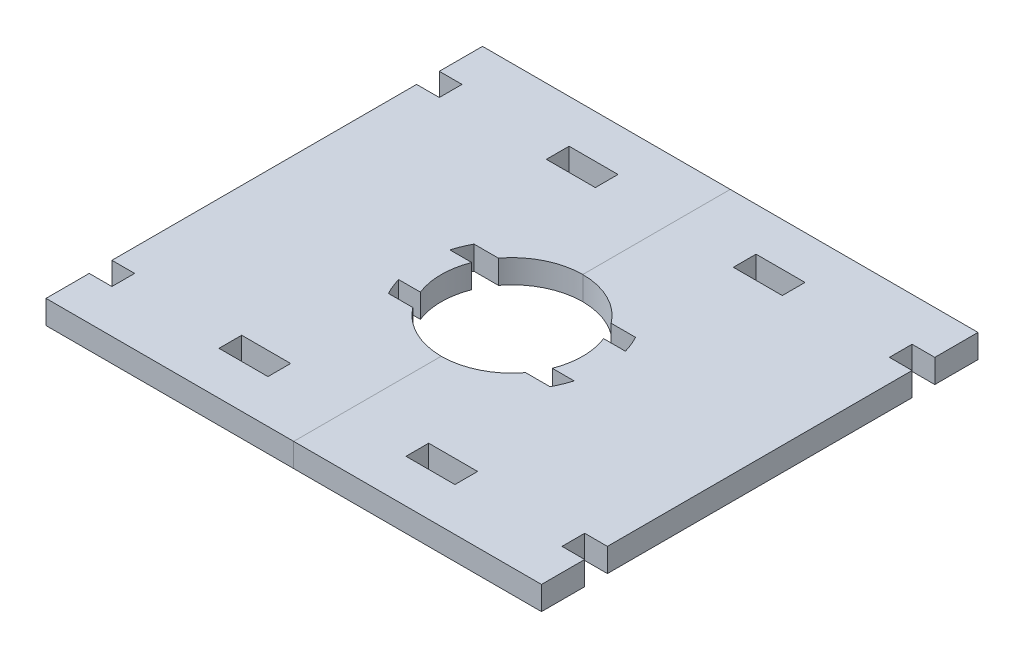
SolidWorks part; units mm, degrees
ref_plane "Front Plane" through (0, 0, 0) normal (0, 0, 1) x (1, 0, 0)
ref_plane "Top Plane" through (0, 0, 0) normal (0, 1, 0) x (1, 0, 0)
ref_plane "Right Plane" through (0, 0, 0) normal (1, 0, 0) x (0, 0, -1)
sketch "Sketch1" plane through (0, 0, 0) normal (0, 1, 0) x (1, 0, 0)
  line L0 (-15.5, 7.25) -> (-13.6999, 7.25) construction
  line L1 (-13.6999, -7.25) -> (-9.5623, -7.25)
  line L2 (-15.5, -7.25) -> (-15.5, -4.35) construction
  line L3 (-13.6999, 7.25) -> (-9.5623, 7.25)
  line L4 (15.5, 4.35) -> (15.5, 7.25) construction
  line L5 (-14.04, -6.5671) -> (-10.8697, -5.0842) construction
  line L6 (-14.04, 6.5671) -> (-10.8697, 5.0842) construction
  line L7 (-14.8771, -4.35) -> (-11.1838, -4.35)
  line L8 (-15.5, -4.35) -> (-15.5, 0) construction
  line L9 (-14.8771, 4.35) -> (-11.1838, 4.35)
  line L10 (15.5, 0) -> (15.5, 4.35) construction
  line L11 (-14.9234, -4.1882) -> (14.9234, 4.1882) construction
  line L12 (-14.9234, 4.1882) -> (14.9234, -4.1882) construction
  line L13 (-15.5, 7.25) -> (-14.04, 6.5671) construction
  line L14 (-15.5, 4.35) -> (-15.5, 7.25) construction
  line L15 (-15.5, 4.35) -> (-14.8771, 4.35) construction
  line L16 (-15.5, 4.35) -> (-14.9234, 4.1882) construction
  line L17 (-15.5, 0) -> (-15.5, 4.35) construction
  line L18 (-15.5, 0) -> (-15.5, 4.35) construction
  line L19 (-15.5, -4.35) -> (-15.5, 0) construction
  line L20 (-15.5, -4.35) -> (-14.9234, -4.1882) construction
  line L21 (-15.5, -4.35) -> (-14.8771, -4.35) construction
  line L22 (-15.5, -7.25) -> (-14.04, -6.5671) construction
  line L23 (-15.5, -7.25) -> (-13.6999, -7.25) construction
  line L24 (15.5, -7.25) -> (15.5, -4.35) construction
  line L25 (14.04, -6.5671) -> (15.5, -7.25) construction
  line L26 (13.6999, -7.25) -> (15.5, -7.25) construction
  line L27 (15.5, -4.35) -> (15.5, 0) construction
  line L28 (15.5, -4.35) -> (15.5, 0) construction
  line L29 (15.5, 0) -> (15.5, 4.35) construction
  line L30 (14.9234, 4.1882) -> (15.5, 4.35) construction
  line L31 (14.8771, 4.35) -> (15.5, 4.35) construction
  line L32 (13.6999, 7.25) -> (15.5, 7.25) construction
  line L33 (14.9234, -4.1882) -> (15.5, -4.35) construction
  line L34 (14.8771, -4.35) -> (15.5, -4.35) construction
  line L35 (-9.5623, 7.25) -> (9.5623, 7.25) construction
  line L36 (9.5623, 7.25) -> (13.6999, 7.25)
  line L37 (-9.3, 4.35) -> (9.3, 4.35) construction
  line L38 (11.1838, 4.35) -> (14.8771, 4.35)
  line L39 (-10.8697, 5.0842) -> (-9.3, 4.35) construction
  line L40 (-9.3, 4.35) -> (9.3, -4.35) construction
  line L41 (-11.1838, 4.35) -> (-9.3, 4.35) construction
  line L42 (-9.5623, -7.25) -> (9.5623, -7.25) construction
  line L43 (9.5623, -7.25) -> (13.6999, -7.25)
  line L44 (-9.3, -4.35) -> (9.3, -4.35) construction
  line L45 (11.1838, -4.35) -> (14.8771, -4.35)
  line L46 (-10.8697, -5.0842) -> (-9.3, -4.35) construction
  line L47 (-9.3, -4.35) -> (9.3, 4.35) construction
  line L48 (-11.1838, -4.35) -> (-9.3, -4.35) construction
  line L49 (9.3, -4.35) -> (11.1838, -4.35) construction
  line L50 (9.3, -4.35) -> (10.8697, -5.0842) construction
  line L51 (10.8697, -5.0842) -> (14.04, -6.5671) construction
  line L52 (9.3, 4.35) -> (11.1838, 4.35) construction
  line L53 (9.3, 4.35) -> (10.8697, 5.0842) construction
  line L54 (10.8697, 5.0842) -> (15.5, 7.25) construction
  arc A0 (-11.1838, 4.35) -> (-11.1838, -4.35) centre (0, 0) ccw
  arc A1 (-13.6999, 7.25) -> (-14.9234, 4.1882) centre (0, 0) ccw
  arc A2 (13.6999, 7.25) -> (-13.6999, 7.25) centre (0, 0) ccw construction
  arc A3 (-13.6999, -7.25) -> (13.6999, -7.25) centre (0, 0) ccw construction
  arc A4 (13.6999, -7.25) -> (14.9234, -4.1882) centre (0, 0) ccw
  arc A5 (15.5, 0) -> (14.9234, 4.1882) centre (0, 0) ccw construction
  arc A6 (14.9234, 4.1882) -> (13.6999, 7.25) centre (0, 0) ccw
  arc A7 (14.9234, -4.1882) -> (15.5, 0) centre (0, 0) ccw construction
  arc A8 (-14.9234, 4.1882) -> (-15.5, 0) centre (0, 0) ccw construction
  arc A9 (-14.9234, -4.1882) -> (-13.6999, -7.25) centre (0, 0) ccw
  arc A10 (-15.5, 0) -> (-14.9234, -4.1882) centre (0, 0) ccw construction
  arc A11 (-9.5623, 7.25) -> (-10.8697, 5.0842) centre (0, 0) ccw construction
  arc A12 (-10.8697, 5.0842) -> (-11.1838, 4.35) centre (0, 0) ccw construction
  arc A13 (-10.8697, -5.0842) -> (-9.5623, -7.25) centre (0, 0) ccw construction
  arc A14 (-9.5623, -7.25) -> (9.5623, -7.25) centre (0, 0) ccw
  arc A15 (-11.1838, -4.35) -> (-10.8697, -5.0842) centre (0, 0) ccw construction
  arc A16 (10.8697, -5.0842) -> (11.1838, -4.35) centre (0, 0) ccw construction
  arc A17 (11.1838, -4.35) -> (-9.5623, 7.25) centre (0, 0) ccw
  arc A18 (9.5623, -7.25) -> (10.8697, -5.0842) centre (0, 0) ccw construction
  dimension "D1" = 24
  dimension "D2" = 31
  dimension "D3" = 14.5
  dimension "D4" = 8.7
sketch "Sketch2" plane through (0, 0, 0) normal (0, 1, 0) x (1, 0, 0)
  line L0 (11.1838, -4.35) -> (14.8771, -4.35) construction
  line L1 (-13.6999, 7.25) -> (-9.5623, 7.25) construction
  line L2 (-14.8771, -4.35) -> (-11.1838, -4.35) construction
  line L3 (-14.8771, 4.35) -> (-11.1838, 4.35) construction
  line L4 (9.5623, -7.25) -> (13.6999, -7.25) construction
  line L5 (-13.6999, -7.25) -> (-9.5623, -7.25) construction
  line L6 (9.5623, 7.25) -> (13.6999, 7.25) construction
  line L7 (11.1838, 4.35) -> (14.8771, 4.35) construction
  line L8 (11.1838, -4.35) -> (14.8771, -4.35)
  line L9 (-13.6999, 7.25) -> (-9.5623, 7.25)
  line L10 (-14.8771, -4.35) -> (-11.1838, -4.35)
  line L11 (-14.8771, 4.35) -> (-11.1838, 4.35)
  line L12 (9.5623, -7.25) -> (13.6999, -7.25)
  line L13 (-13.6999, -7.25) -> (-9.5623, -7.25)
  line L14 (9.5623, 7.25) -> (13.6999, 7.25)
  line L15 (11.1838, 4.35) -> (14.8771, 4.35)
  line L17 (-42, -37) -> (42, -37)
  line L18 (-42, -37) -> (-42, 37)
  line L19 (-42, 37) -> (42, 37)
  line L20 (42, -37) -> (42, 37)
  line L21 (-42, -37) -> (42, 37) construction
  line L22 (-42, 37) -> (42, -37) construction
  arc A0 (11.1838, -4.35) -> (-9.5623, 7.25) centre (0, 0) ccw construction
  arc A1 (-13.6999, 7.25) -> (-14.9234, 4.1882) centre (0, 0) ccw construction
  arc A2 (-11.1838, 4.35) -> (-11.1838, -4.35) centre (0, 0) ccw construction
  arc A3 (13.6999, -7.25) -> (14.9234, -4.1882) centre (0, 0) ccw construction
  arc A4 (-9.5623, -7.25) -> (9.5623, -7.25) centre (0, 0) ccw construction
  arc A5 (-14.9234, -4.1882) -> (-13.6999, -7.25) centre (0, 0) ccw construction
  arc A6 (14.9234, 4.1882) -> (13.6999, 7.25) centre (0, 0) ccw construction
  arc A7 (11.1838, -4.35) -> (-9.5623, 7.25) centre (0, 0) ccw
  arc A8 (-13.6999, 7.25) -> (-14.9234, 4.1882) centre (0, 0) ccw
  arc A9 (-11.1838, 4.35) -> (-11.1838, -4.35) centre (0, 0) ccw
  arc A10 (13.6999, -7.25) -> (14.9234, -4.1882) centre (0, 0) ccw
  arc A11 (-9.5623, -7.25) -> (9.5623, -7.25) centre (0, 0) ccw
  arc A12 (-14.9234, -4.1882) -> (-13.6999, -7.25) centre (0, 0) ccw
  arc A13 (14.9234, 4.1882) -> (13.6999, 7.25) centre (0, 0) ccw
  dimension "D1" = 84
  dimension "D2" = 74
extrude "Boss-Extrude1" add sketch "Sketch2" along normal blind 4
split "Split1" trim tools "Right Plane" bodies to split 101 resulting bodies 102 103
sketch "Sketch4" plane through (0, 4, 0) normal (0, 1, 0) x (1, 0, 0)
  line L0 (0, -18.5) -> (42, -18.5) construction
  line L2 (42, -37) -> (42, 37) construction
  line L3 (0, -18.5) -> (0, -37) construction
  line L4 (-42, -37) -> (-42, 37) construction
  line L5 (-20, -29.675) -> (-11.7, -29.675)
  line L6 (-20, -29.675) -> (-20, -25.825)
  line L7 (-20, -25.825) -> (-11.7, -25.825)
  line L8 (-11.7, -29.675) -> (-11.7, -25.825)
  line L9 (-20, -29.675) -> (-11.7, -25.825) construction
  line L10 (-20, -25.825) -> (-11.7, -29.675) construction
  line L11 (-42, -29.675) -> (-38.15, -29.675)
  line L12 (-42, -29.675) -> (-42, -25.825)
  line L13 (-42, -25.825) -> (-38.15, -25.825)
  line L14 (-38.15, -29.675) -> (-38.15, -25.825)
  line L15 (-42, -29.675) -> (-38.15, -25.825) construction
  line L16 (-42, -25.825) -> (-38.15, -29.675) construction
  line L17 (0, 0) -> (0, -37) construction
  line L33 (42, -25.825) -> (38.15, -29.675) construction
  line L34 (42, -29.675) -> (38.15, -25.825) construction
  line L35 (20, -25.825) -> (11.7, -29.675) construction
  line L36 (20, -29.675) -> (11.7, -25.825) construction
  line L45 (38.15, -29.675) -> (38.15, -25.825)
  line L46 (42, -25.825) -> (38.15, -25.825)
  line L47 (42, -29.675) -> (42, -25.825)
  line L48 (42, -29.675) -> (38.15, -29.675)
  line L49 (11.7, -29.675) -> (11.7, -25.825)
  line L50 (20, -25.825) -> (11.7, -25.825)
  line L51 (20, -29.675) -> (20, -25.825)
  line L52 (20, -29.675) -> (11.7, -29.675)
  line L53 (-2.2, 0) -> (2.2, 0) construction
  line L54 (20, 29.675) -> (11.7, 25.825) construction
  line L55 (20, 25.825) -> (11.7, 29.675) construction
  line L56 (42, 29.675) -> (38.15, 25.825) construction
  line L57 (42, 25.825) -> (38.15, 29.675) construction
  line L58 (20, 29.675) -> (11.7, 29.675)
  line L59 (20, 29.675) -> (20, 25.825)
  line L60 (20, 25.825) -> (11.7, 25.825)
  line L61 (11.7, 29.675) -> (11.7, 25.825)
  line L62 (42, 29.675) -> (38.15, 29.675)
  line L63 (42, 29.675) -> (42, 25.825)
  line L64 (42, 25.825) -> (38.15, 25.825)
  line L65 (38.15, 29.675) -> (38.15, 25.825)
  line L82 (-42, 25.825) -> (-38.15, 29.675) construction
  line L83 (-42, 29.675) -> (-38.15, 25.825) construction
  line L84 (-20, 25.825) -> (-11.7, 29.675) construction
  line L85 (-20, 29.675) -> (-11.7, 25.825) construction
  line L94 (-38.15, 29.675) -> (-38.15, 25.825)
  line L95 (-42, 25.825) -> (-38.15, 25.825)
  line L96 (-42, 29.675) -> (-42, 25.825)
  line L97 (-42, 29.675) -> (-38.15, 29.675)
  line L98 (-11.7, 29.675) -> (-11.7, 25.825)
  line L99 (-20, 25.825) -> (-11.7, 25.825)
  line L100 (-20, 29.675) -> (-20, 25.825)
  line L101 (-20, 29.675) -> (-11.7, 29.675)
  point P6 (-15.85, -27.75)
  point P14 (0, -27.75)
  point P15 (-40.075, -27.75)
  point P53 (40.075, -27.75)
  point P54 (15.85, -27.75)
  point P65 (15.85, 27.75)
  point P66 (40.075, 27.75)
  point P95 (-40.075, 27.75)
  point P96 (-15.85, 27.75)
  dimension "D1" = 3.85
  dimension "D2" = 8.3
  dimension "D3" = 20
  dimension "D4" = 3.85
extrude "Cut-Extrude2" cut sketch "Sketch4" against normal through all both
equation "\"m3_hole\"= 3.5"
equation "\"m3_washer\"= 7.3"
equation "\"m3_nut\"= 5.3"
equation "\"guide_width\"= 10.0"
equation "\"guide_length\"= 65.0"
equation "\"guide_tab_length\" = 10.0"
equation "\"guide_tab_width\" = 9.0"
equation "\"guide_thickness\" = 12.0"
equation "\"grinder_od\"= 52.0"
equation "\"grinder_id\"= 45.5"
equation "\"grinder_adjust_od\" = 58.0"
equation "\"funnel_width_from_adjust_ring\" = 13.0"
equation "\"drill_contact_diameter_small\" = 24.0"
equation "\"drill_contact_diameter_medium\" = 28.0"
equation "\"drill_contact_diameter_large\" = 39.0"
equation "\"drill_contact_diameter_tab\" = 31.0"
equation "\"drill_contact_ow_tab\" = 14.5"
equation "\"drill_contact_iw_tab\" = 8.7"
equation "\"drill_contact_small_height\" = 15.5"
equation "\"drill_contact_large_height\" = 34.5"
equation "\"D1@Sketch1\"=\"drill_contact_diameter_small\""
equation "\"D2@Sketch1\"=\"drill_contact_diameter_tab\""
equation "\"D3@Sketch1\"=\"drill_contact_ow_tab\""
equation "\"D1@Sketch2\"=\"grinder_od\"+\"guide_thickness\"+20"
equation "\"D2@Sketch2\"=\"grinder_od\"+\"guide_thickness\"+\"guide_tab_length\""
equation "\"plywood_thickness\" = 3.85"
equation "\"D4@Sketch1\"=\"drill_contact_iw_tab\""
equation "\"plywood_peg_length\" = 40"
equation "\"plywood_peg_width\" = 8.3"
equation "\"D3@Sketch4\"=\"plywood_peg_length\"/2"
equation "\"D2@Sketch4\"=\"plywood_peg_width\""
equation "\"D1@Sketch4\"=\"plywood_thickness\""
equation "\"D4@Sketch4\"=\"plywood_thickness\""
